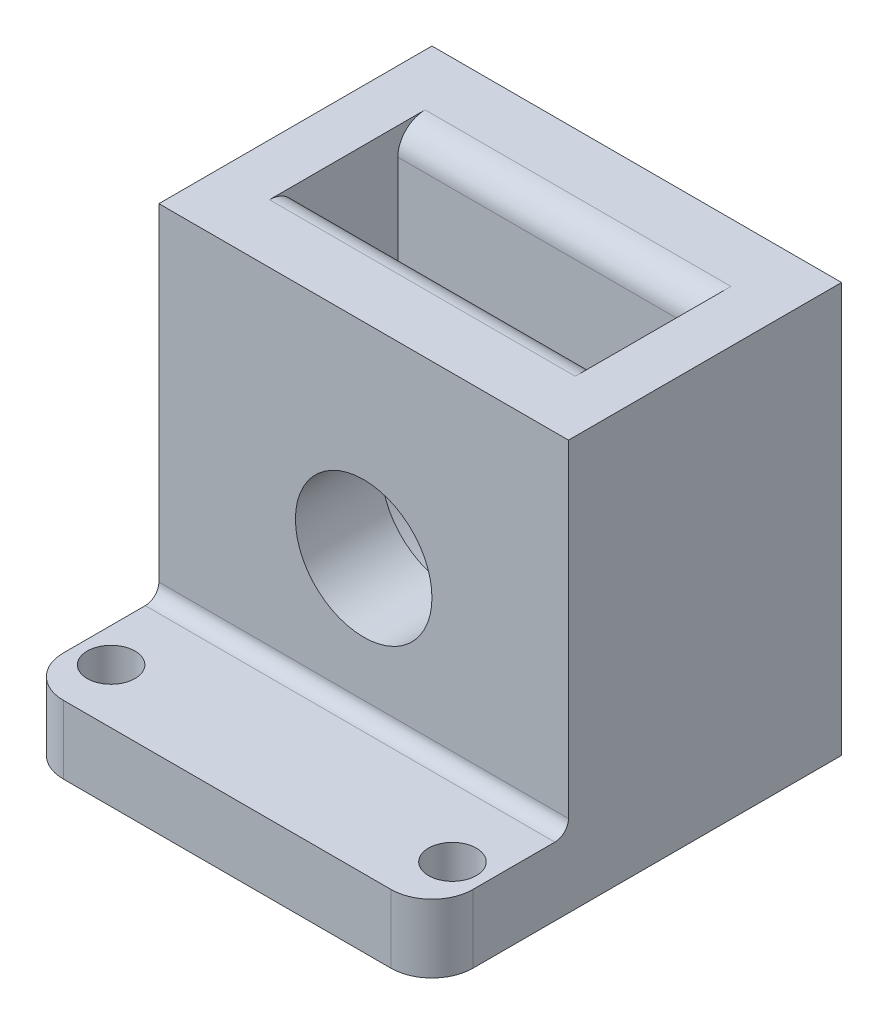
SolidWorks part; units mm, degrees
ref_plane "Front Plane" through (0, 0, 0) normal (0, 0, 1) x (1, 0, 0)
ref_plane "Top Plane" through (0, 0, 0) normal (0, 1, 0) x (1, 0, 0)
ref_plane "Right Plane" through (0, 0, 0) normal (1, 0, 0) x (0, 0, -1)
sketch "Sketch2" plane through (0, 0, 0) normal (0, 0, 1) x (1, 0, 0)
  line L0 (-15, 15) -> (15, -15) construction
  line L1 (-15, -15) -> (15, -15)
  line L2 (-15, -15) -> (-15, 15)
  line L3 (-15, 15) -> (15, 15)
  line L4 (15, -15) -> (15, 15)
  circle A0 centre (0, 0) radius 5
  dimension "D1" = 10
  dimension "D2" = 30
  dimension "D3" = 30
  dimension "D4" = 15
extrude "Boss-Extrude1" add sketch "Sketch2" along normal blind 20
sketch "Sketch3" plane through (0, 0, 0) normal (0, 0, 1) x (1, 0, 0)
  line L0 (-11.2, 15) -> (-11.2, 0)
  line L1 (15, 15) -> (-15, 15) construction
  line L2 (11.2, 15) -> (11.2, 0)
  line L3 (0, 0) -> (0, 15) construction
  line L9 (11.2, 15) -> (-11.2, 15)
  line L11 (-15, -15) -> (15, -15) construction
  arc A2 (-11.2, 0) -> (11.2, 0) centre (0, 0) ccw
  circle A3 centre (0, 0) radius 5 construction
  point P12 (0, 0)
  point P13 (0, 0)
  point P14 (0, 0)
  point P15 (0, 0)
  dimension "D1" = 22.4
  dimension "D2" = 15
ref_plane "Plane1" through (0, 0, 10) normal (0, 0, -1) x (-1, 0, 0)
extrude "Cut-Extrude2" cut sketch "Sketch3" along normal mid plane 7.4 from surface at 10 starting at plane "Plane1"
sketch "Sketch4" plane through (0, -15, 0) normal (0, -1, 0) x (1, 0, 0)
  line L5 (0, 26) -> (0, 0) construction
  line L7 (-15, 20) -> (-15, 30)
  line L8 (15, 20) -> (15, 30)
  line L9 (-15, 30) -> (15, 30)
  line L10 (-15, 20) -> (15, 20)
  line L11 (-12.5, 26) -> (12.5, 26) construction
  circle A2 centre (-12.5, 26) radius 1.75
  circle A4 centre (12.5, 26) radius 1.75
  dimension "D1" = 10
  dimension "D2" = 3.5
  dimension "D3" = 3.5
  dimension "D4" = 25
  dimension "D5" = 6
extrude "Boss-Extrude2" add sketch "Sketch4" against normal blind 5
fillet "Fillet2" radius 3 2 edges at (15, -12.5, 30) (-15, -12.5, 30)
fillet "Fillet3" radius 1 1 edges at (0, -10, 20)
fillet "Fillet4" radius 2 2 edges at (0, 15, 13.7) (0, 15, 6.3)
equation "\"centdist\"= \"RD1@Annotations\""
